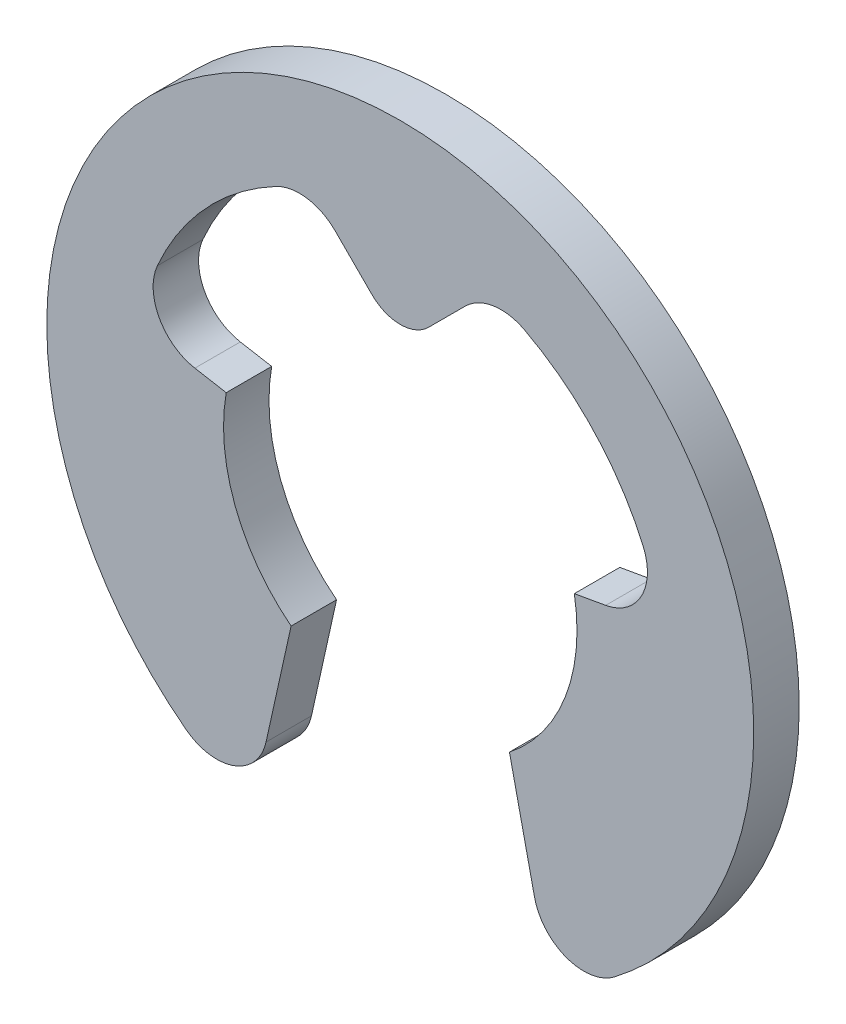
SolidWorks part; units mm, degrees
ref_plane "Plan1" through (0, 0, 0) normal (0, 0, 1) x (1, 0, 0)
ref_plane "Plan2" through (0, 0, 0) normal (0, 1, 0) x (1, 0, 0)
ref_plane "Plan3" through (0, 0, 0) normal (1, 0, 0) x (0, 0, -1)
sketch "Esquisse1" plane through (0, 0, 0) normal (0, 0, 1) x (1, 0, 0)
  line L0 (0, 0) -> (0, 4.2932) construction
  line L1 (0.5609, 3.7323) -> (1.2882, 4.4596)
  line L2 (-0.5609, 3.7323) -> (-1.2882, 4.4596)
  line L3 (-2.6582, -4.9904) -> (-2.162, -2.7524)
  line L4 (2.162, -2.7524) -> (2.6582, -4.9904)
  line L5 (0, 0) -> (8.1749, 0) construction
  line L6 (3.4468, 0.6078) -> (4.0679, 0.7173)
  line L7 (-3.4468, 0.6078) -> (-4.0679, 0.7173)
  arc A0 (4.2402, -5.5696) -> (-4.2402, -5.5696) centre (0, 0) ccw
  arc A1 (2.162, -2.7524) -> (3.4468, 0.6078) centre (0, 0) ccw
  arc A2 (-2.4647, 4.6355) -> (-4.8106, 2.1026) centre (0, 0) ccw
  arc A3 (-0.5609, 3.7323) -> (0.5609, 3.7323) centre (0, 4.2932) ccw
  arc A4 (-2.4647, 4.6355) -> (-1.2882, 4.4596) centre (-1.9953, 3.7525) cw
  arc A5 (2.4647, 4.6355) -> (1.2882, 4.4596) centre (1.9953, 3.7525) ccw
  arc A6 (4.8106, 2.1026) -> (2.4647, 4.6355) centre (0, 0) ccw
  arc A7 (-3.4468, 0.6078) -> (-2.162, -2.7524) centre (0, 0) ccw
  arc A8 (-4.0679, 0.7173) -> (-4.8106, 2.1026) centre (-3.8943, 1.7021) cw
  arc A9 (4.8106, 2.1026) -> (4.0679, 0.7173) centre (3.8943, 1.7021) cw
  arc A10 (-2.6582, -4.9904) -> (-4.2402, -5.5696) centre (-3.6345, -4.7739) cw
  arc A11 (4.2402, -5.5696) -> (2.6582, -4.9904) centre (3.6345, -4.7739) cw
  point P13 (0, 7)
  dimension "D1" = 7
  dimension "D2" = 14
  dimension "D3" = 10.5
  dimension "D5" = 1
  dimension "D8" = 1
  dimension "D9" = 1
  dimension "D4" = 90
  dimension "D6" = 25
  dimension "D7" = 10
extrude "Base-Extrusion" add sketch "Esquisse1" along normal blind 0.9
equation "\"D3@Esquisse1\" = (\"D2@Esquisse1\"+\"D1@Esquisse1\")/2"
